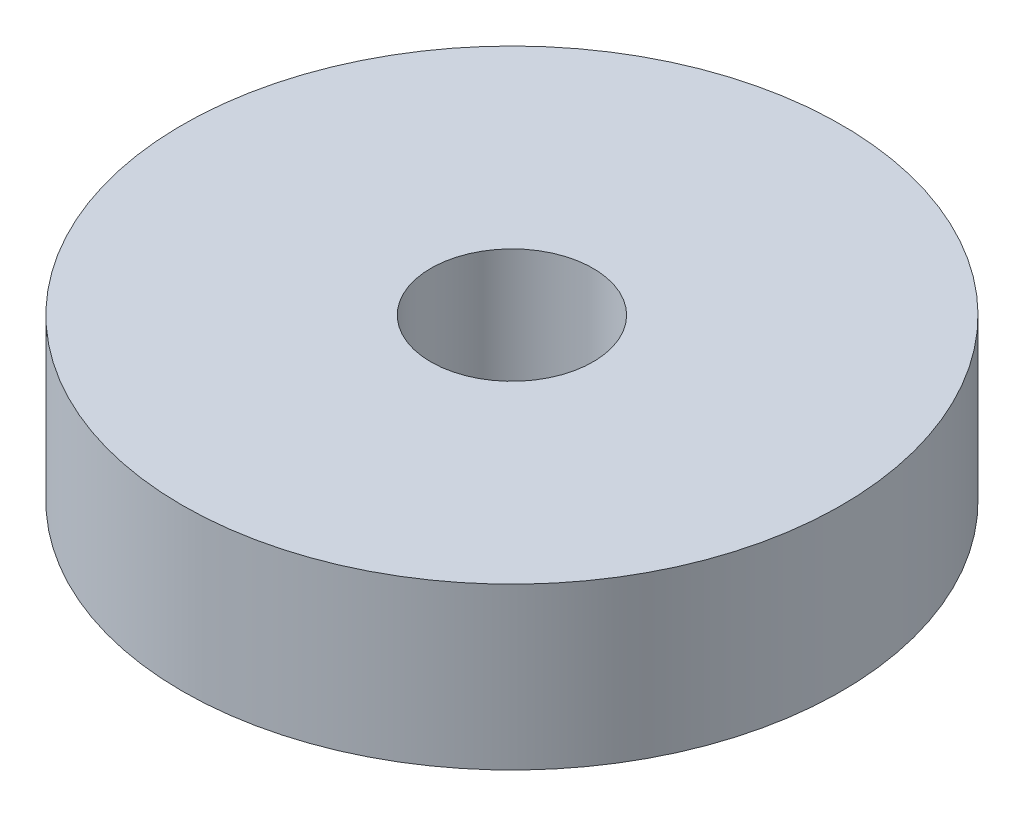
SolidWorks part; units mm, degrees
ref_plane "Front Plane" through (0, 0, 0) normal (0, 0, 1) x (1, 0, 0)
ref_plane "Top Plane" through (0, 0, 0) normal (0, 1, 0) x (1, 0, 0)
ref_plane "Right Plane" through (0, 0, 0) normal (1, 0, 0) x (0, 0, -1)
sketch "Sketch1" plane through (0, 0, 0) normal (0, 1, 0) x (1, 0, 0)
  circle A0 centre (0, 0) radius 1.6
  circle A1 centre (0, 0) radius 6.5
  dimension "D1" = 3.2
  dimension "D2" = 13
extrude "Boss-Extrude1" add sketch "Sketch1" along normal mid plane 3.175
